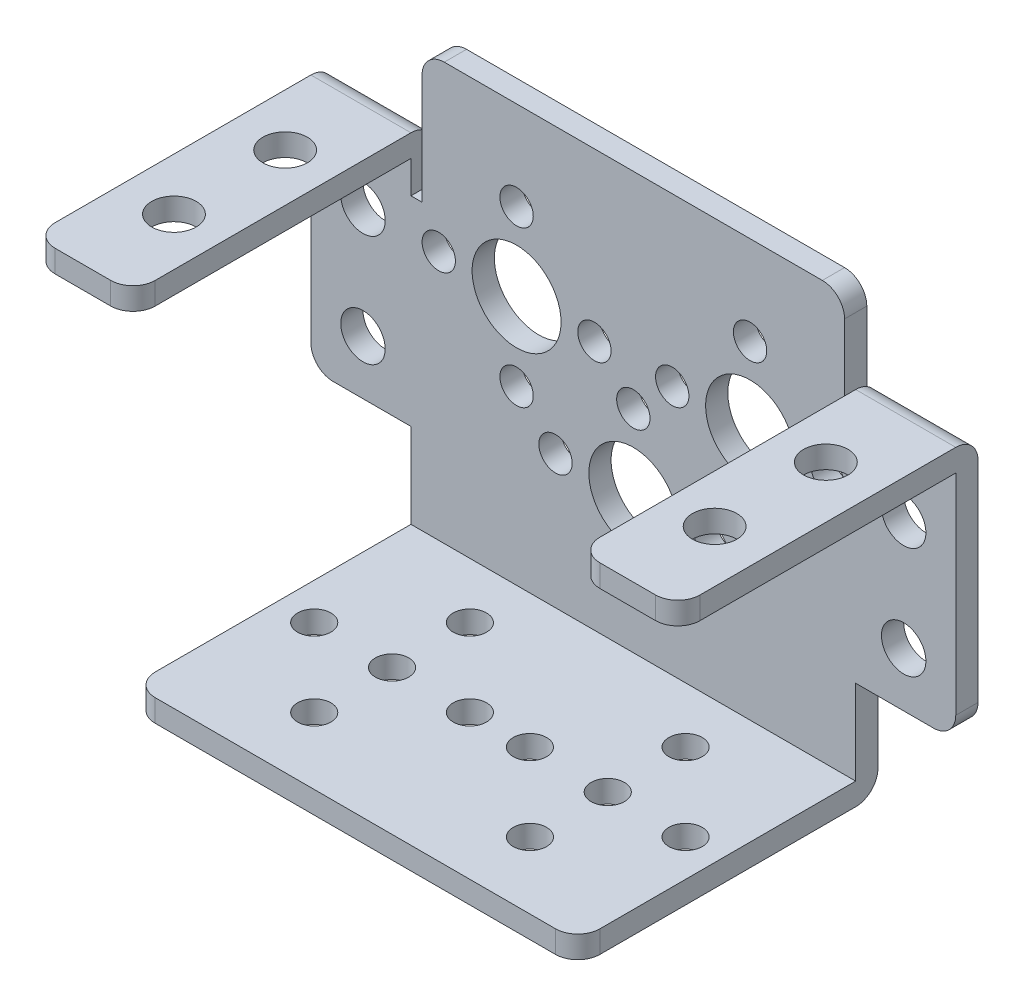
SolidWorks part; units mm, degrees
ref_plane "前视基准面" through (0, 0, 0) normal (0, 0, 1) x (1, 0, 0)
ref_plane "上视基准面" through (0, 0, 0) normal (0, 1, 0) x (1, 0, 0)
ref_plane "右视基准面" through (0, 0, 0) normal (1, 0, 0) x (0, 0, -1)
sketch "草图1" plane through (0, 0, 0) normal (0, 0, 1) x (1, 0, 0)
  line L0 (0, 40.2276) -> (0, -60.0469) construction
  line L1 (-47.2005, 0) -> (47.4773, 0) construction
  line L2 (-11.4903, -6.75) -> (7.7209, -6.75) construction
  line L3 (-17, 18.75) -> (17, 18.75)
  line L4 (-29, 7.75) -> (-29, -9.1241)
  line L5 (-18, -18.75) -> (18, -18.75)
  line L6 (29, 7.75) -> (29, -9.1241)
  line L7 (-35.0412, 3.75) -> (46.0471, 3.75) construction
  line L8 (-19, 42.3016) -> (-19, -30.3365) construction
  line L9 (-20, 42.3016) -> (-20, -28.6406) construction
  line L10 (-19, 16.75) -> (-19, 6.8385)
  line L11 (-19, 6.8385) -> (-20, 6.8385)
  line L12 (-20, 6.8385) -> (-20, 9.75)
  line L13 (-20, 9.75) -> (-27, 9.75)
  line L14 (-27, -11.1241) -> (-20, -11.1241)
  line L15 (-20, -11.1241) -> (-20, -16.75)
  line L16 (-24.315, 17.9851) -> (-24.315, -14.5149) construction
  line L17 (20, -11.1241) -> (20, -16.75)
  line L18 (27, -11.1241) -> (20, -11.1241)
  line L19 (19, 6.8385) -> (20, 6.8385)
  line L20 (20, 6.8385) -> (20, 9.75)
  line L21 (20, 9.75) -> (27, 9.75)
  line L22 (19, 16.75) -> (19, 6.8385)
  line L23 (-20, -16.75) -> (-20, -18.75)
  line L24 (-20, -18.75) -> (-18, -18.75)
  line L25 (20, -16.75) -> (20, -18.75)
  line L26 (20, -18.75) -> (18, -18.75)
  line L27 (29, 7.75) -> (29, 9.75)
  line L28 (29, 9.75) -> (27, 9.75)
  line L29 (-29, 7.75) -> (-29, 9.75)
  line L30 (-29, 9.75) -> (-27, 9.75)
  circle A0 centre (0, -6.75) radius 4
  circle A1 centre (-10.5, 3.75) radius 4
  circle A2 centre (-7, -6.75) radius 1.5
  circle A3 centre (0, 0.25) radius 1.5
  circle A4 centre (7, -6.75) radius 1.5
  circle A5 centre (0, -13.75) radius 1.5
  circle A6 centre (-17.5, 3.75) radius 1.5
  circle A7 centre (10.5, -3.25) radius 1.5
  circle A8 centre (-10.5, 10.75) radius 1.5
  circle A9 centre (-3.5, 3.75) radius 1.5
  circle A10 centre (-10.5, -3.25) radius 1.5
  circle A11 centre (17.5, 3.75) radius 1.5
  circle A12 centre (3.5, 3.75) radius 1.5
  circle A13 centre (10.5, 3.75) radius 4
  circle A14 centre (10.5, 10.75) radius 1.5
  circle A15 centre (-24.315, -6.25) radius 2
  circle A16 centre (-24.315, 3.75) radius 2
  arc A17 (-27, -11.1241) -> (-29, -9.1241) centre (-27, -9.1241) cw
  arc A19 (-19, 16.75) -> (-17, 18.75) centre (-17, 16.75) cw
  circle A20 centre (24.315, 3.75) radius 2
  circle A21 centre (24.315, -6.25) radius 2
  arc A22 (27, -11.1241) -> (29, -9.1241) centre (27, -9.1241) ccw
  arc A24 (19, 16.75) -> (17, 18.75) centre (17, 16.75) ccw
  point P25 (0, -6.75)
  point P38 (-10.5, 3.75)
  point P67 (-19, 18.75)
  point P70 (-20, -18.75)
  dimension "D5" = 8
  dimension "D7" = 3
  dimension "D11" = 4
  dimension "D16" = 4
  dimension "D18" = 10
  dimension "D19" = 2
  dimension "D21" = 2
  dimension "D3" = 18.75
  dimension "D4" = 29
  dimension "D6" = 12
  dimension "D9" = 22.5
  dimension "D10" = 21
  dimension "D12" = 19
  dimension "D13" = 1
  dimension "D14" = 28.5
  dimension "D15" = 48.63
  dimension "D17" = 12.5
  dimension "D8" = 4
extrude "凸台-拉伸1" add sketch "草图1" along normal blind 2
sketch "草图2" plane through (0, -18.75, 0) normal (0, -1, 0) x (1, 0, 0)
  line L0 (20, 2) -> (20, 0) construction
  line L1 (-20, 0) -> (20, 0)
  line L2 (-20, 0) -> (-20, 25)
  line L3 (-18, 27) -> (18, 27)
  line L4 (20, 0) -> (20, 25)
  line L5 (0, 33.5575) -> (0, -14.0158) construction
  line L6 (-34.9581, 14) -> (38.4138, 14) construction
  circle A0 centre (9.7, 14) radius 1.5
  circle A1 centre (-9.7, 14) radius 1.5
  circle A2 centre (-2.7, 14) radius 1.5
  circle A3 centre (16.7, 14) radius 1.5
  circle A4 centre (9.7, 7) radius 1.5
  circle A5 centre (2.7, 14) radius 1.5
  circle A6 centre (9.7, 21) radius 1.5
  circle A7 centre (-9.7, 7) radius 1.5
  circle A8 centre (-16.7, 14) radius 1.5
  circle A9 centre (-9.7, 21) radius 1.5
  arc A10 (-20, 25) -> (-18, 27) centre (-18, 25) cw
  arc A11 (20, 25) -> (18, 27) centre (18, 25) ccw
  point P27 (9.7, 14)
  point P34 (-20, 27)
  dimension "D4" = 3
  dimension "D5" = 10.3
  dimension "D6" = 4
  dimension "D7" = 2
  dimension "D8" = 2
  dimension "D1" = 27
  dimension "D2" = 20
  dimension "D3" = 14
extrude "凸台-拉伸2" add sketch "草图2" along normal blind 2
fillet "圆角2" radius 2 1 edges at (0, -20.75, 0)
sketch "草图3" plane through (0, 9.75, 0) normal (0, 1, 0) x (1, 0, 0)
  line L0 (0, 0) -> (0, -28.8215) construction
  line L1 (29, 0) -> (20, 0)
  line L2 (29, 0) -> (29, -25)
  line L3 (27, -27) -> (22, -27)
  line L4 (20, 0) -> (20, -25)
  line L5 (36.3668, -14) -> (16.4985, -14) construction
  line L6 (-36.3668, -14) -> (-16.4985, -14) construction
  line L7 (-29, 0) -> (-20, 0)
  line L8 (-29, 0) -> (-29, -25)
  line L9 (-27, -27) -> (-22, -27)
  line L10 (-20, 0) -> (-20, -25)
  circle A0 centre (24.315, -9) radius 2
  circle A1 centre (24.315, -19) radius 2
  circle A2 centre (-24.315, -19) radius 2
  circle A3 centre (-24.315, -9) radius 2
  arc A4 (20, -25) -> (22, -27) centre (22, -25) ccw
  arc A5 (29, -25) -> (27, -27) centre (27, -25) cw
  arc A6 (-20, -25) -> (-22, -27) centre (-22, -25) cw
  arc A7 (-29, -25) -> (-27, -27) centre (-27, -25) ccw
  point P26 (20, -27)
  point P29 (29, -27)
  point P32 (-20, -27)
  point P35 (-29, -27)
  dimension "D1" = 4
  dimension "D6" = 2
  dimension "D7" = 2
  dimension "D8" = 2
  dimension "D2" = 14
  dimension "D3" = 10
  dimension "D4" = 27
  dimension "D5" = 48.63
extrude "凸台-拉伸3" add sketch "草图3" along normal blind 2
fillet "圆角3" radius 2 1 edges at (24.5, 11.75, 0)
fillet "圆角4" radius 2 1 edges at (-24.5, 11.75, 0)
